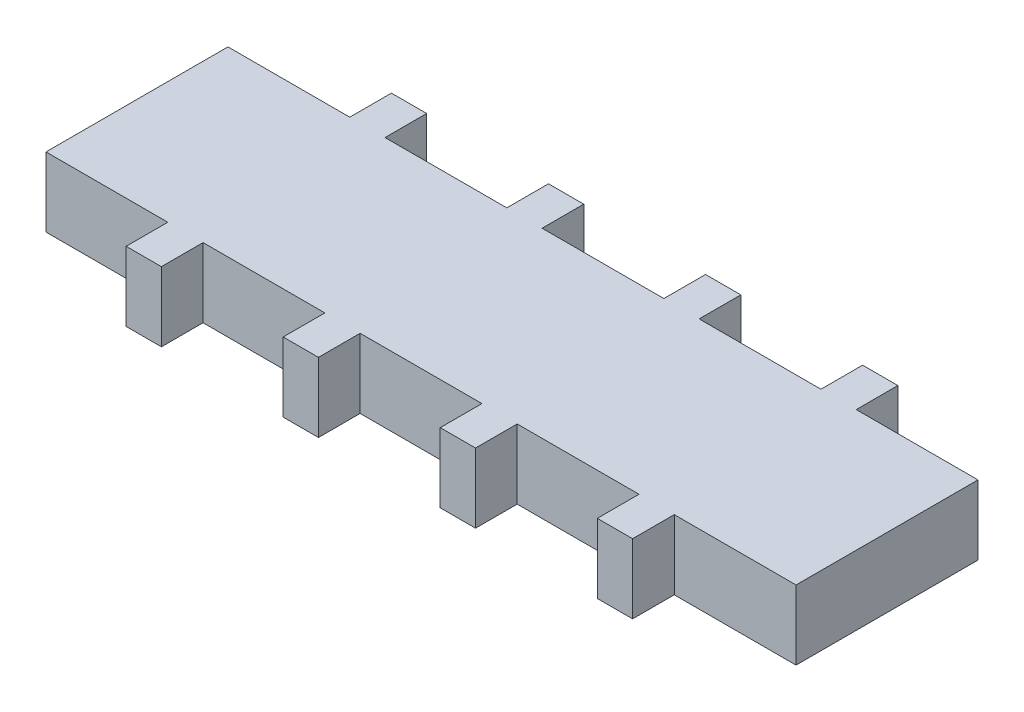
SolidWorks part; units mm, degrees
ref_plane "Front Plane" through (0, 0, 0) normal (0, 0, 1) x (1, 0, 0)
ref_plane "Top Plane" through (0, 0, 0) normal (0, 1, 0) x (1, 0, 0)
ref_plane "Right Plane" through (0, 0, 0) normal (1, 0, 0) x (0, 0, -1)
sketch "Sketch1" plane through (0, 0, 0) normal (0, 1, 0) x (1, 0, 0)
  line L0 (-15.692, 8.05) -> (-6.924, 8.05) construction
  line L1 (-27, 6.55) -> (27, 6.55)
  line L2 (-27, 6.55) -> (-27, -6.55)
  line L3 (-27, -6.55) -> (27, -6.55)
  line L4 (27, 6.55) -> (27, -6.55)
  line L5 (-27, 6.55) -> (27, -6.55) construction
  line L6 (-27, -6.55) -> (27, 6.55) construction
  line L7 (-18.232, 6.55) -> (-15.692, 6.55)
  line L8 (-18.232, 6.55) -> (-18.232, 9.55)
  line L9 (-18.232, 9.55) -> (-15.692, 9.55)
  line L10 (-15.692, 6.55) -> (-15.692, 9.55)
  line L11 (-4.384, 6.55) -> (-6.924, 6.55)
  line L12 (-4.384, 6.55) -> (-4.384, 9.55)
  line L13 (-4.384, 9.55) -> (-6.924, 9.55)
  line L14 (-6.924, 6.55) -> (-6.924, 9.55)
  line L15 (4.384, 6.55) -> (6.924, 6.55)
  line L16 (4.384, 6.55) -> (4.384, 9.55)
  line L17 (4.384, 9.55) -> (6.924, 9.55)
  line L18 (6.924, 6.55) -> (6.924, 9.55)
  line L19 (15.692, 6.55) -> (18.232, 6.55)
  line L20 (15.692, 6.55) -> (15.692, 9.55)
  line L21 (15.692, 9.55) -> (18.232, 9.55)
  line L22 (18.232, 6.55) -> (18.232, 9.55)
  line L23 (-18.232, -6.55) -> (-15.692, -6.55)
  line L24 (-18.232, -6.55) -> (-18.232, -9.55)
  line L25 (-18.232, -9.55) -> (-15.692, -9.55)
  line L26 (-15.692, -6.55) -> (-15.692, -9.55)
  line L27 (-6.924, -6.55) -> (-4.384, -6.55)
  line L28 (-6.924, -6.55) -> (-6.924, -9.55)
  line L29 (-6.924, -9.55) -> (-4.384, -9.55)
  line L30 (-4.384, -6.55) -> (-4.384, -9.55)
  line L31 (4.384, -6.55) -> (6.924, -6.55)
  line L32 (4.384, -6.55) -> (4.384, -9.55)
  line L33 (4.384, -9.55) -> (6.924, -9.55)
  line L34 (6.924, -6.55) -> (6.924, -9.55)
  line L35 (15.692, -6.55) -> (18.232, -6.55)
  line L36 (15.692, -6.55) -> (15.692, -9.55)
  line L37 (15.692, -9.55) -> (18.232, -9.55)
  line L38 (18.232, -6.55) -> (18.232, -9.55)
  line L39 (-4.384, 8.05) -> (4.384, 8.05) construction
  line L40 (6.924, 8.05) -> (15.692, 8.05) construction
  line L41 (18.232, 8.05) -> (27, 8.05) construction
  line L42 (27, 8.05) -> (27, 6.55) construction
  line L43 (-18.232, 8.05) -> (-27, 8.05) construction
  line L44 (-27, 8.05) -> (-27, 6.55) construction
  line L45 (-18.232, -8.05) -> (-27, -8.05) construction
  line L46 (-27, -8.05) -> (-27, -6.55) construction
  line L47 (-15.692, -8.05) -> (-6.924, -8.05) construction
  line L48 (-4.384, -8.05) -> (4.384, -8.05) construction
  line L49 (6.924, -8.05) -> (15.692, -8.05) construction
  line L50 (18.232, -8.05) -> (27, -8.05) construction
  line L51 (27, -8.05) -> (27, -6.55) construction
  point P0 (0, 0)
  dimension "D1" = 54
  dimension "D2" = 2.54
  dimension "D3" = 19.1
  dimension "D4" = 3
extrude "Boss-Extrude1" add sketch "Sketch1" along normal blind 5 contours L4 L1 L2 L3 | L26 L3 L24 L25 | L30 L3 L28 L29 | L34 L3 L32 L33 | L38 L3 L36 L37 | L1 L22 L21 L20 | L1 L18 L17 L16 | L14 L1 L12 L13 | L1 L10 L9 L8
